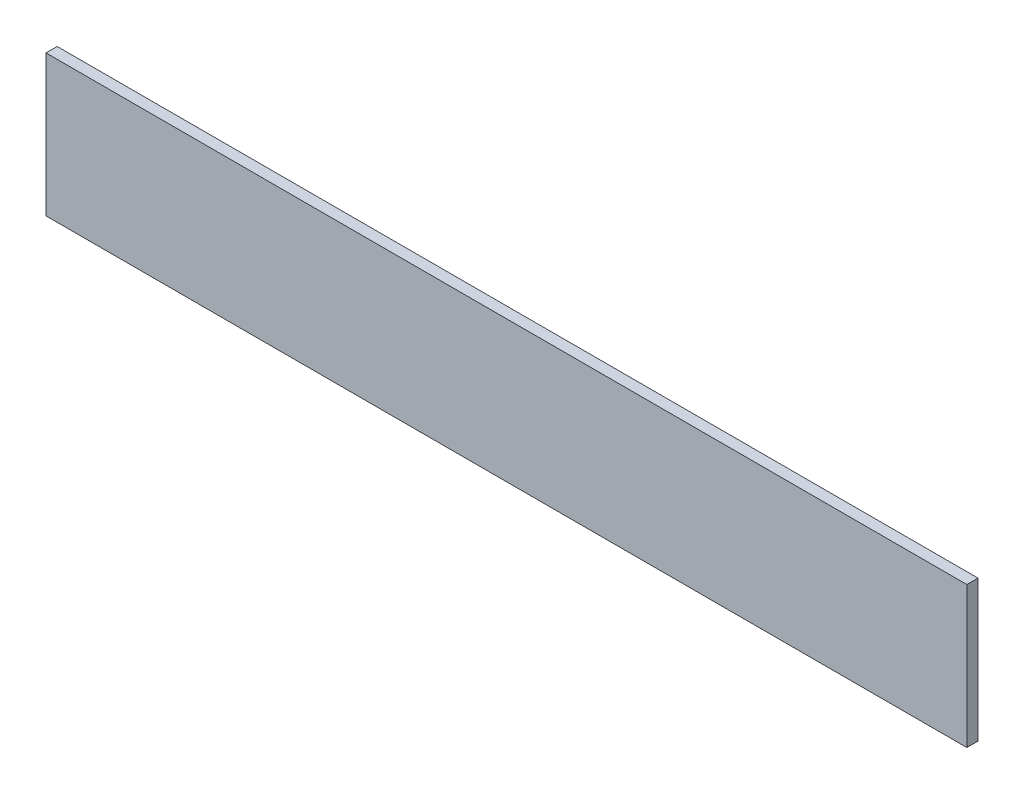
SolidWorks part; units mm, degrees
ref_plane "Front Plane" through (0, 0, 0) normal (0, 0, 1) x (1, 0, 0)
ref_plane "Top Plane" through (0, 0, 0) normal (0, 1, 0) x (1, 0, 0)
ref_plane "Right Plane" through (0, 0, 0) normal (1, 0, 0) x (0, 0, -1)
sketch "Sketch1" plane through (0, 0, 0) normal (0, 0, 1) x (1, 0, 0)
  line L1 (-391.0263, 114.4781) -> (533.3737, 114.4781)
  line L2 (-391.0263, 114.4781) -> (-391.0263, -27.2539)
  line L3 (-391.0263, -27.2539) -> (533.3737, -27.2539)
  line L4 (533.3737, 114.4781) -> (533.3737, -27.2539)
  dimension "D1" = 924.4
  dimension "D2" = 141.732
extrude "Boss-Extrude1" add sketch "Sketch1" along normal blind 11.2
